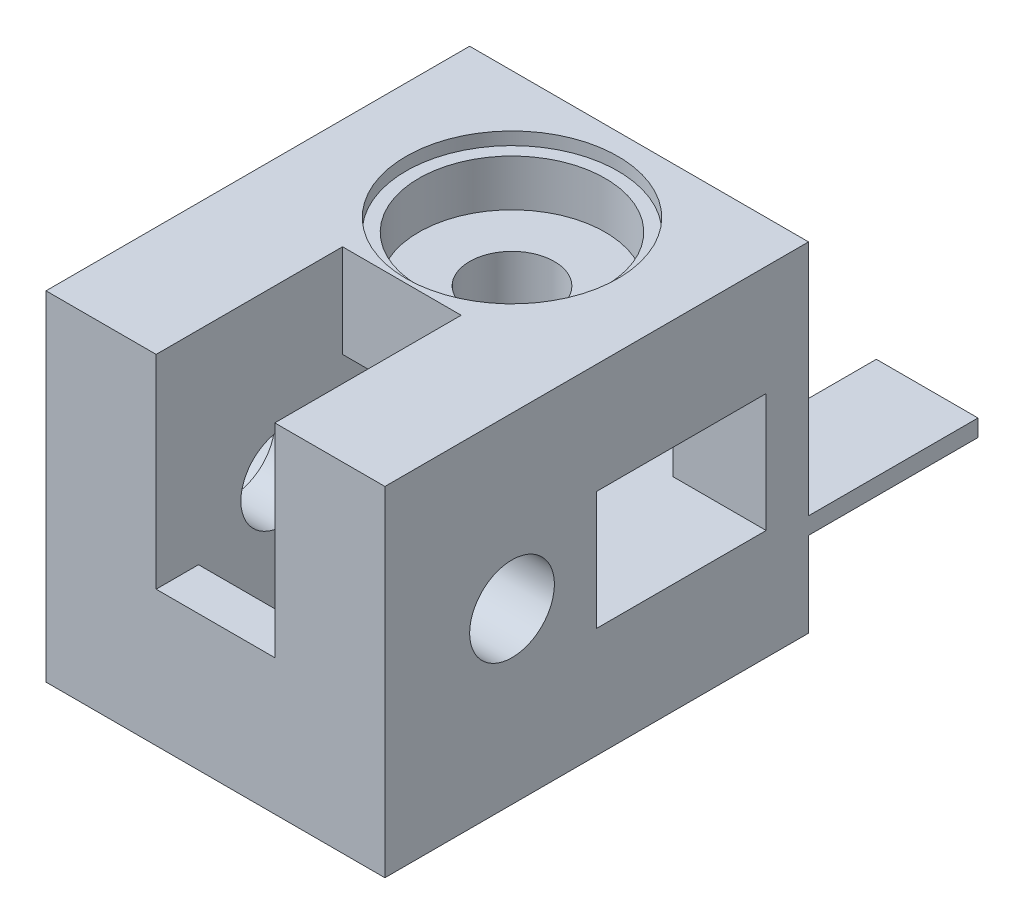
SolidWorks part; units mm, degrees
ref_plane "Plan de face" through (0, 0, 0) normal (0, 0, 1) x (1, 0, 0)
ref_plane "Plan de dessus" through (0, 0, 0) normal (0, 1, 0) x (1, 0, 0)
ref_plane "Plan de droite" through (0, 0, 0) normal (1, 0, 0) x (0, 0, -1)
sketch "Esquisse1" plane through (0, 0, 0) normal (0, 0, 1) x (1, 0, 0)
  line L1 (-40, 40) -> (0, 40)
  line L2 (-40, 40) -> (-40, 0)
  line L3 (-40, 0) -> (0, 0)
  line L4 (0, 40) -> (0, 0)
  dimension "D1" = 40
  dimension "D2" = 40
extrude "Boss.-Extru.1" add sketch "Esquisse1" along normal blind 50
sketch "Esquisse2" plane through (0, 40, 0) normal (0, 1, 0) x (1, 0, 0)
  line L0 (0, 0) -> (-40, 0) construction
  line L1 (-40, -50) -> (-40, 0) construction
  circle A0 centre (-20, -15) radius 5
  dimension "D1" = 10
  dimension "D2" = 15
  dimension "D3" = 20
extrude "Enlèv. mat.-Extru.1" cut sketch "Esquisse2" against normal through all
sketch "Esquisse3" plane through (-40, 0, 0) normal (-1, 0, 0) x (0, 0, 1)
  line L0 (50, 40) -> (50, 0) construction
  line L1 (50, 40) -> (0, 40) construction
  circle A0 centre (35, 20) radius 5
  dimension "D1" = 10
  dimension "D2" = 15
  dimension "D3" = 20
extrude "Enlèv. mat.-Extru.2" cut sketch "Esquisse3" against normal through all
sketch "Esquisse4" plane through (-40, 0, 0) normal (-1, 0, 0) x (0, 0, 1)
  line L1 (22, 27) -> (0, 27)
  line L2 (22, 27) -> (22, 13)
  line L3 (22, 13) -> (0, 13)
  line L4 (0, 27) -> (0, 13)
  line L5 (0, 40) -> (0, 0) construction
  line L6 (50, 0) -> (0, 0) construction
  line L7 (50, 40) -> (0, 40) construction
  dimension "D1" = 14
  dimension "D2" = 22
  dimension "D3" = 0
  dimension "D4" = 13
  dimension "D5" = 13
extrude "Enlèv. mat.-Extru.3" cut sketch "Esquisse4" against normal blind 29
sketch "Esquisse5" plane through (0, 0, 0) normal (0, -1, 0) x (1, 0, 0)
  line L0 (-40, 50) -> (0, 50) construction
  line L1 (-13, 25) -> (-27, 25)
  line L2 (-13, 25) -> (-13, 45)
  line L3 (-13, 45) -> (-27, 45)
  line L4 (-27, 25) -> (-27, 45)
  line L5 (-40, 50) -> (-40, 0) construction
  dimension "D1" = 20
  dimension "D2" = 5
  dimension "D3" = 14
  dimension "D4" = 13
extrude "Enlèv. mat.-Extru.4" cut sketch "Esquisse5" against normal blind 29
sketch "Esquisse6" plane through (0, 0, 0) normal (1, 0, 0) x (0, 0, -1)
  line L1 (-5, 27) -> (-25, 27)
  line L2 (0, 0) -> (0, 40) construction
  line L3 (-5, 13) -> (-25, 13)
  line L4 (-25, 27) -> (-25, 13)
  line L5 (-50, 0) -> (0, 0) construction
  line L6 (-5, 27) -> (-5, 13)
  dimension "D1" = 14
  dimension "D2" = 5
  dimension "D3" = 13
  dimension "D4" = 20
extrude "Enlèv. mat.-Extru.5" cut sketch "Esquisse6" against normal blind 24
sketch "Esquisse7" plane through (0, 40, 0) normal (0, 1, 0) x (1, 0, 0)
  line L0 (0, -50) -> (-40, -50) construction
  line L1 (-27, -50) -> (-13, -50)
  line L2 (-27, -50) -> (-27, -28)
  line L3 (-27, -28) -> (-13, -28)
  line L4 (-13, -50) -> (-13, -28)
  line L5 (-40, -50) -> (-40, 0) construction
  dimension "D1" = 14
  dimension "D2" = 22
  dimension "D3" = 13
extrude "Enlèv. mat.-Extru.6" cut sketch "Esquisse7" against normal blind 24
sketch "Esquisse10" plane through (0, 40, 0) normal (0, 1, 0) x (1, 0, 0)
  circle A0 centre (-20, -15) radius 11
  dimension "D1" = 22
extrude "Enlèv. mat.-Extru.9" cut sketch "Esquisse10" against normal blind 7
sketch "Esquisse11" plane through (0, 40, 0) normal (0, 1, 0) x (1, 0, 0)
  circle A0 centre (-20, -15) radius 12.5
  dimension "D1" = 25
extrude "Enlèv. mat.-Extru.10" cut sketch "Esquisse11" against normal blind 1.5
sketch "Esquisse13" plane through (0, 0, 50) normal (0, 0, 1) x (1, 0, 0)
  line L3 (-40, 0) -> (0, 0) construction
  line L8 (-10, 0) -> (-10, 10)
  line L9 (-10, 10) -> (0, 10)
  line L10 (0, 0) -> (0, 40) construction
  line L11 (0, 10) -> (0, 12)
  line L12 (0, 12) -> (-12, 12)
  line L13 (-12, 12) -> (-12, 0)
  line L14 (-12, 0) -> (-10, 0)
  dimension "D5" = 12
  dimension "D6" = 12
  dimension "D7" = 2
  dimension "D8" = 2
sketch "Esquisse14" plane through (-40, 0, 0) normal (-1, 0, 0) x (0, 0, 1)
  circle A0 centre (35, 20) radius 11
  dimension "D1" = 22
extrude "Enlèv. mat.-Extru.11" cut sketch "Esquisse14" against normal blind 7
sketch "Esquisse15" plane through (-40, 0, 0) normal (-1, 0, 0) x (0, 0, 1)
  circle A0 centre (35, 20) radius 12.5
  dimension "D1" = 25
extrude "Enlèv. mat.-Extru.12" cut sketch "Esquisse15" against normal blind 1.5
sketch "Esquisse16" plane through (0, 0, 0) normal (0, 0, -1) x (-1, 0, 0)
  line L0 (12, 0) -> (12, 12)
  line L1 (12, 12) -> (0, 12)
  line L2 (0, 12) -> (0, 10)
  line L3 (0, 10) -> (10, 10)
  line L4 (10, 10) -> (10, 0)
  line L5 (10, 0) -> (12, 0)
extrude "Boss.-Extru.2" add sketch "Esquisse16" along normal blind 20
